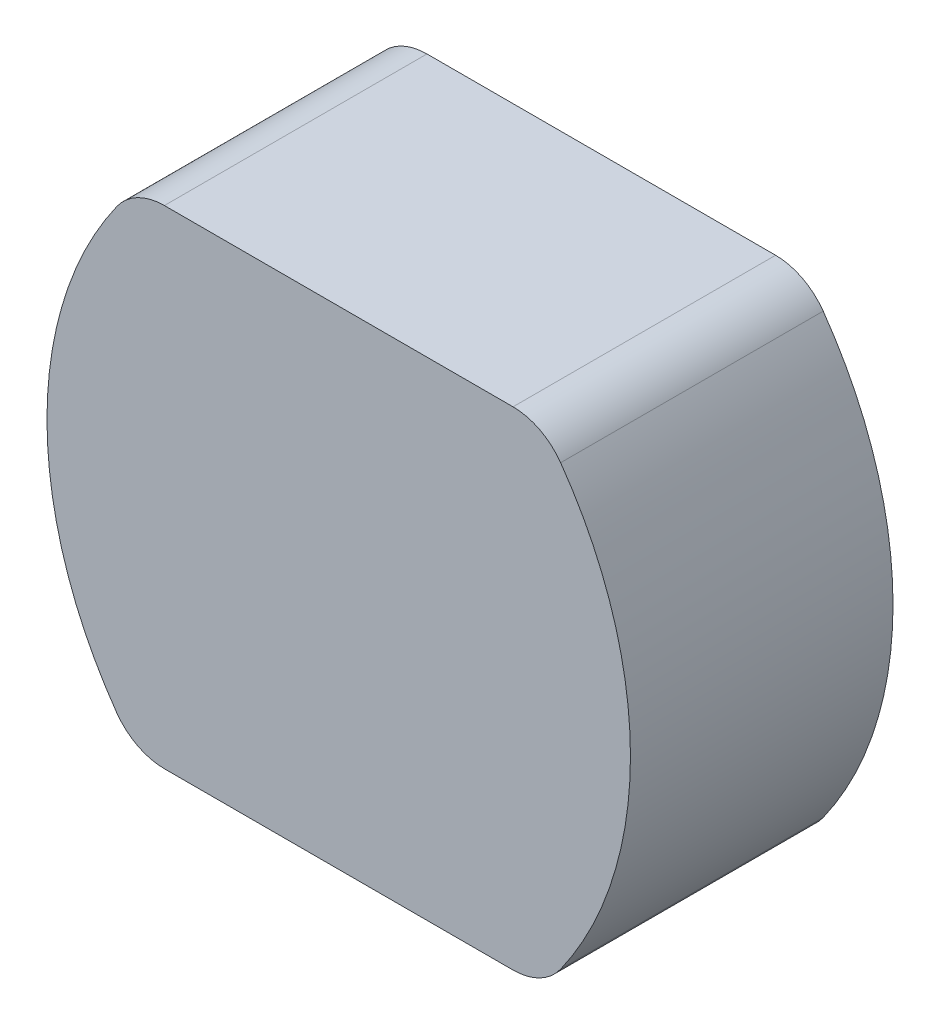
SolidWorks part; units mm, degrees
ref_plane "Front Plane" through (0, 0, 0) normal (0, 0, 1) x (1, 0, 0)
ref_plane "Top Plane" through (0, 0, 0) normal (0, 1, 0) x (1, 0, 0)
ref_plane "Right Plane" through (0, 0, 0) normal (1, 0, 0) x (0, 0, -1)
sketch "Sketch1" plane through (0, 0, 0) normal (0, 0, 1) x (1, 0, 0)
  line L0 (-10, 0) -> (10, 0)
  line L1 (0, 8.36) -> (0, 0) construction
  line L2 (-6.9554, 8.36) -> (6.9554, 8.36)
  line L4 (-6.9554, -8.36) -> (6.9554, -8.36)
  line L6 (-10, 0) -> (10, 0) construction
  arc A0 (-6.9554, -8.36) -> (-6.9554, 8.36) centre (3, 0) cw
  arc A1 (6.9554, -8.36) -> (6.9554, 8.36) centre (-3, 0) ccw
  point P10 (-10, 0)
  dimension "D5" = 13
  dimension "D1" = 8.36
  dimension "D3" = 10
  dimension "D2" = 13.9108
extrude "Boss-Extrude1" add sketch "Sketch1" along normal blind 9 contours L0 A1 L2 A0 | L4 A1 L0 A0
fillet "Fillet2" radius 2 2 edges at (6.9554, 8.36, 4.5) (-6.9554, 8.36, 4.5)
fillet "Fillet3" radius 2 2 edges at (-6.9554, -8.36, 4.5) (6.9554, -8.36, 4.5)
